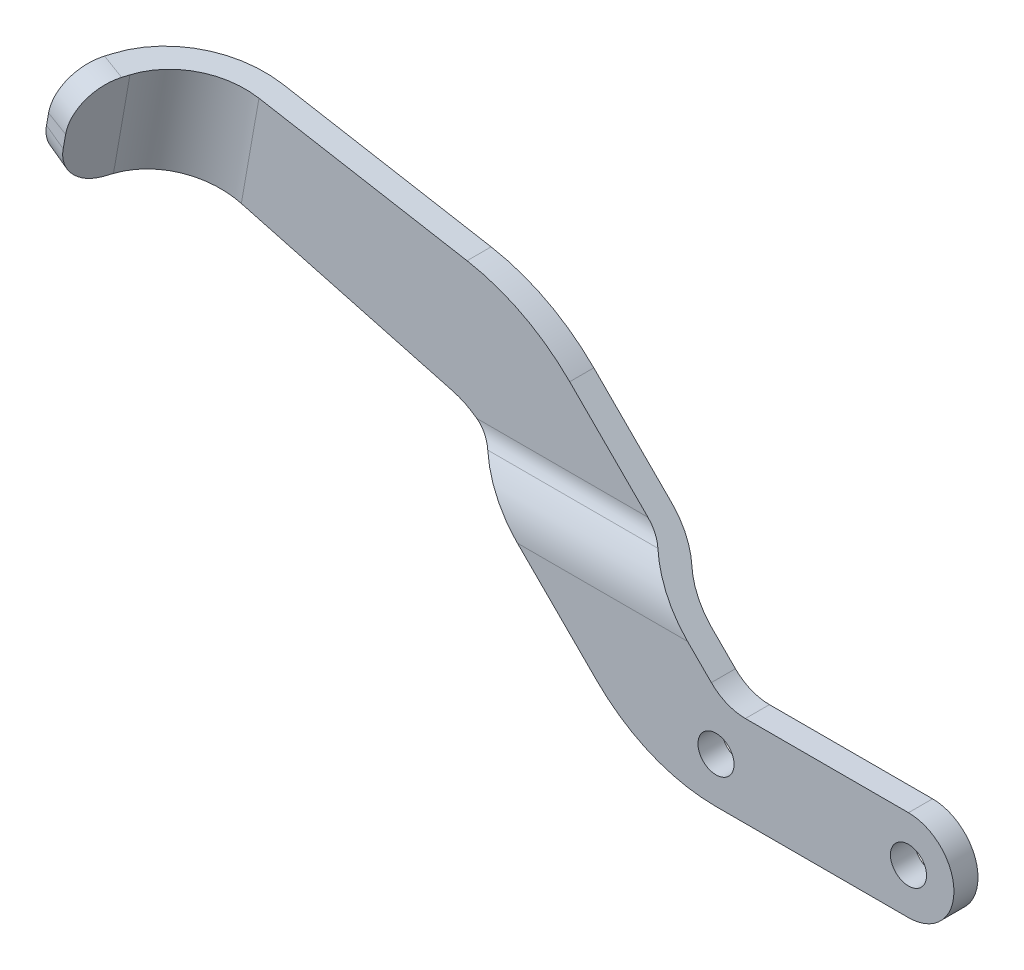
SolidWorks part; units mm, degrees
ref_plane "front" through (0, 0, 0) normal (0, 0, 1) x (1, 0, 0)
ref_plane "top" through (0, 0, 0) normal (0, 1, 0) x (1, 0, 0)
ref_plane "side" through (0, 0, 0) normal (1, 0, 0) x (0, 0, -1)
other "Configuration Table"
sketch "Sketch1" plane through (0, 0, 0) normal (0, 0, 1) x (1, 0, 0)
  line L0 (0, 6) -> (-21.525, 6)
  line L1 (0, -6) -> (-25.4, -6)
  line L2 (-26.0151, 7.8599) -> (-47.8835, 29.7283)
  line L3 (-59.1089, 18.503) -> (-41.1154, 0.5096)
  line L4 (-63.3788, 20.9682) -> (-91.2266, 28.43)
  line L5 (-61.4334, 36.7819) -> (-88.9, 41.625)
  line L6 (-91.2266, 28.43) -> (-88.9, 41.625)
  arc A0 (0, 6) -> (0, -6) centre (0, 0) cw
  arc A1 (-25.4, -6) -> (-41.1154, 0.5096) centre (-25.4, 16.225) cw
  arc A2 (-26.0151, 7.8599) -> (-21.525, 6) centre (-21.525, 12.35) ccw
  arc A3 (-59.1089, 18.503) -> (-63.3788, 20.9682) centre (-65.8441, 11.7678) ccw
  arc A4 (-47.8835, 29.7283) -> (-61.4334, 36.7819) centre (-65.8441, 11.7678) ccw
  dimension "D6" = 22.225
  dimension "D7" = 6.35
  dimension "D10" = 25.4
  dimension "D8" = 25.4
  dimension "D1" = 15
  dimension "D2" = 12
  dimension "D3" = 15.875
  dimension "D4" = 5
  dimension "D5" = 135
  dimension "D9" = 88.9
  dimension "D11" = 47.625
extrude "Base-Extrude" add sketch "Sketch1" along normal mid plane 6.35
sketch "Sketch2" plane through (0, 0, 0) normal (1, 0, 0) x (0, 0, -1)
  line L0 (3.175, -6) -> (3.175, 30.3525) construction
  line L1 (0, -6) -> (0, 10.9997)
  line L2 (-3.175, -6) -> (3.175, -6) construction
  line L3 (3.175, 29.7283) -> (3.175, 36.7819) construction
  line L4 (0, -6) -> (3.175, -6)
  arc A0 (0, 10.9997) -> (1.5875, 15.1999) centre (6.35, 10.9997) cw
  arc A2 (1.5875, 15.1999) -> (3.175, 19.4) centre (-3.175, 19.4) ccw
  dimension "D1" = 6.35
  dimension "D2" = 6.35
  dimension "D3" = 25.4
  dimension "D4" = 3.175
extrude "Cut-Extrude1" cut sketch "Sketch2" against normal through all and the other way through all flip side to cut
sketch "Sketch3" plane through (0, 0, 0) normal (1, 0, 0) x (0, 0, -1)
  line L0 (-3.175, 7.8599) -> (-3.175, 29.7283) construction
  line L1 (0, 19.4) -> (0, 41.625)
  line L2 (-3.175, 41.625) -> (3.175, 41.625) construction
  line L3 (0, 41.625) -> (-3.175, 41.625)
  line L4 (-3.175, 41.625) -> (-3.175, 10.9997)
  line L7 (3.175, 19.4) -> (3.175, 42.0866) construction
  arc A0 (1.5875, 15.1999) -> (3.175, 19.4) centre (-3.175, 19.4) ccw construction
  arc A1 (0, 19.4) -> (-0.7938, 17.2999) centre (-3.175, 19.4) cw
  arc A2 (-0.7938, 17.2999) -> (-3.175, 10.9997) centre (6.35, 10.9997) ccw
  arc A3 (1.5875, 15.1999) -> (0, 10.9997) centre (6.35, 10.9997) ccw construction
extrude "Cut-Extrude2" cut sketch "Sketch3" against normal through all
sketch "Sketch4" plane through (0, 0, 3.175) normal (0, 0, 1) x (1, 0, 0)
  line L0 (0, 0) -> (-25.4, 0) construction
  circle A0 centre (0, 0) radius 2.3813
  circle A1 centre (-25.4, 0) radius 2.3813
  dimension "D1" = 4.7625
  dimension "D2" = 25.4
extrude "Cut-Extrude3" cut sketch "Sketch4" against normal through all
sketch "Sketch6" plane through (4.4376, 25.1671, 0) normal (0.1736, 0.9848, 0) x (-0.9848, 0.1736, 0)
  line L1 (94.7775, -3.175) -> (94.7775, 0)
  line L2 (107.5081, 6.7355) -> (109.0409, 12.793)
  line L3 (109.0409, 12.793) -> (105.9629, 13.5718)
  line L4 (105.9629, 13.5718) -> (104.4301, 7.5143)
  line L5 (66.8872, -3.175) -> (94.7775, -3.175) construction
  line L7 (94.7775, 0) -> (94.7775, -3.175) construction
  line L8 (94.7775, 0) -> (66.8872, 0) construction
  arc A0 (94.7775, -3.175) -> (107.5081, 6.7355) centre (94.7775, 9.9568) ccw
  arc A1 (94.7775, 0) -> (104.4301, 7.5143) centre (94.7775, 9.9568) ccw
  dimension "D1" = 13.1318
  dimension "D3" = 6.2484
  dimension "D4" = 104.2
extrude "Boss-Extrude1" add sketch "Sketch6" against normal up to surface (13.3985 mm away)
fillet "Fillet4" radius 5.334 2 edges at (-103.5644, 31.7359, 13.1824) (-101.431, 43.8346, 13.1824)
